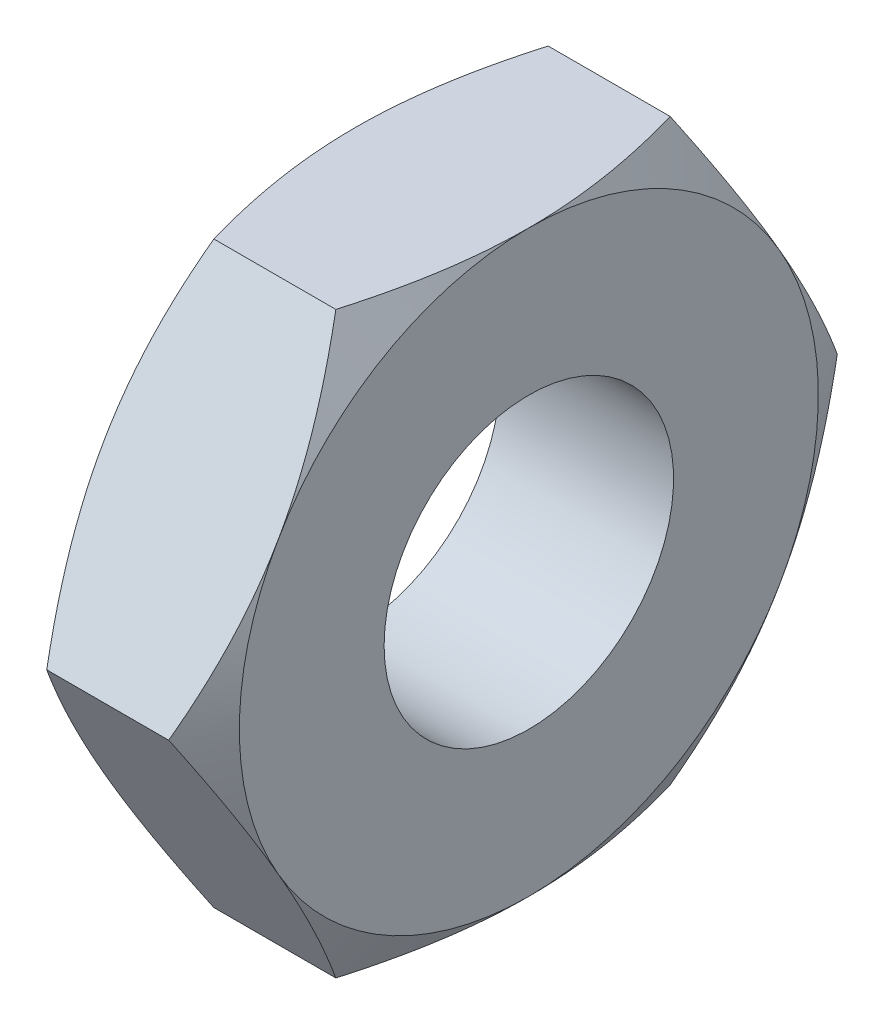
SolidWorks part; units mm, degrees
material "Alloy Steel (SS)"
ref_plane "Front Plane" through (0, 0, 0) normal (0, 0, 1) x (1, 0, 0)
ref_plane "Top Plane" through (0, 0, 0) normal (0, 1, 0) x (1, 0, 0)
ref_plane "Right Plane" through (0, 0, 0) normal (1, 0, 0) x (0, 0, -1)
sketch "Sketch1" plane through (0, 0, 0) normal (1, 0, 0) x (0, 0, -1)
  line L1 (5.7735, 0) -> (2.8868, 5)
  line L2 (2.8868, 5) -> (-2.8868, 5)
  line L3 (-2.8868, 5) -> (-5.7735, 0)
  line L4 (-5.7735, 0) -> (-2.8868, -5)
  line L5 (-2.8868, -5) -> (2.8868, -5)
  line L6 (2.8868, -5) -> (5.7735, 0)
  circle A0 centre (0, 0) radius 5 construction
  dimension "A/F" = 10
extrude "Boss-Extrude1" add sketch "Sketch1" along normal blind 3
hole_wizard " Tapped Hole1" positions "Sketch5" profile "Sketch4" tap size "M6x1.0" standard "Ansi Metric" end condition through all
sketch "Sketch5" plane through (0, 0, 0) normal (-1, 0, 0) x (0, 0, 1)
  point P0 (0, 0)
sketch "Sketch4" plane through (0, 0, 0) normal (0, 1, 0) x (0, 0, 1)
  line L0 (0, 0) -> (0, 3)
  line L1 (0, 3) -> (2.5, 3)
  line L2 (2.5, 3) -> (2.5, 0)
  line L5 (2.5, 0) -> (0, 0)
  line L11 (0, -6.35) -> (0, 107.95) construction
  dimension "Thru Tap Drill Dia." = 5
  dimension "Thru Tap Drill Depth" = 3
cosmetic thread "Hole Thread1" parameters "D2"=6
sketch "Sketch6" plane through (0, 0, 0) normal (0, 1, 0) x (1, 0, 0)
  line L0 (0, 0) -> (10.1923, 0) construction
  line L1 (0, 5) -> (0.4466, 5.7735)
  line L2 (3, 5.7735) -> (0, 5.7735) construction
  line L3 (0, 5.7735) -> (0, 2.8868) construction
  line L5 (0.4466, 5.7735) -> (0, 5.7735)
  line L6 (0, 5.7735) -> (0, 5)
  dimension "D1" = 5
  dimension "D2" = 30
revolve "Cut-Revolve1" cut sketch "Sketch6" angle 360 about L0
ref_plane "Plane1" through (1.5, 0, 0) normal (-1, 0, 0) x (0, 0, 1)
mirror "Mirror1" about plane through (1.5, 0, 0) normal (-1, 0, 0) of "Cut-Revolve1"
